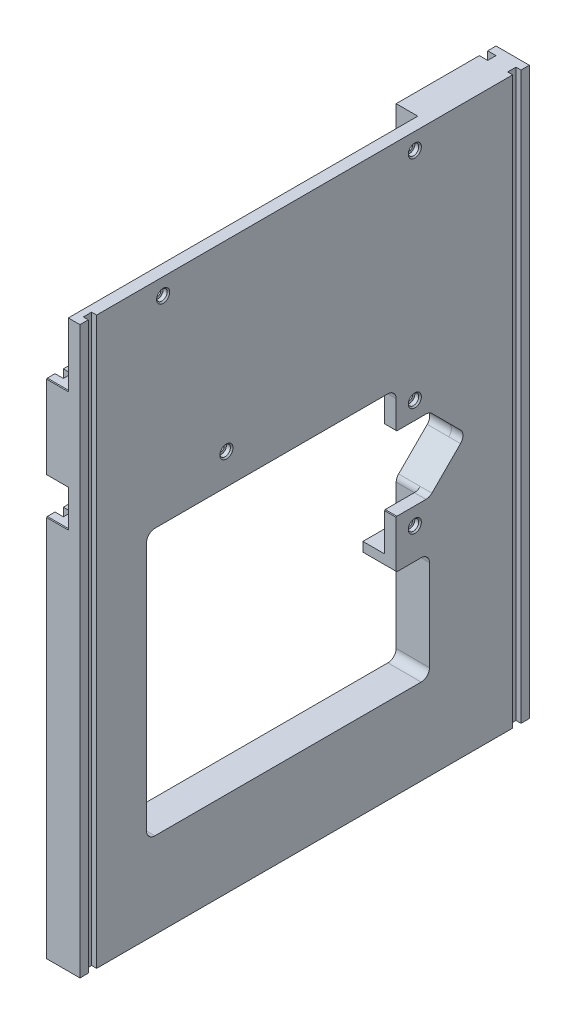
SolidWorks part; units mm, degrees
ref_plane "Front Plane" through (0, 0, 0) normal (0, 0, 1) x (1, 0, 0)
ref_plane "Top Plane" through (0, 0, 0) normal (0, 1, 0) x (1, 0, 0)
ref_plane "Right Plane" through (0, 0, 0) normal (1, 0, 0) x (0, 0, -1)
sketch "Sketch2" plane through (0, 0, 0) normal (1, 0, 0) x (0, 0, -1)
  line L1 (-215.489, 137.2751) -> (127.411, 137.2751)
  line L2 (-215.489, 137.2751) -> (-215.489, -294.5249)
  line L3 (-215.489, -294.5249) -> (127.411, -294.5249)
  line L4 (127.411, 137.2751) -> (127.411, -294.5249)
  dimension "D1" = 342.9
  dimension "D2" = 431.8
extrude "Base" add sketch "Sketch2" along normal blind 25.4
sketch "Sketch3" plane through (0, 0, 0) normal (1, 0, 0) x (0, 0, -1)
  line L0 (-44.039, -294.5249) -> (-44.039, 137.2751) construction
  line L1 (-215.489, -294.5249) -> (127.411, -294.5249) construction
  line L2 (-164.689, -25.9199) -> (-164.689, -229.1199)
  line L3 (-164.689, -229.1199) -> (51.211, -229.1199)
  line L4 (51.211, -146.9509) -> (51.211, -229.1199)
  line L5 (127.411, 137.2751) -> (-215.489, 137.2751) construction
  line L7 (-215.489, 137.2751) -> (-215.489, -294.5249) construction
  line L9 (51.211, -146.9509) -> (25.811, -146.9509)
  line L13 (-164.689, -25.9199) -> (25.811, -25.9199)
  line L14 (25.811, -146.9509) -> (25.811, -25.9199)
  dimension "D1" = 25.4
  dimension "D2" = 163.195
  dimension "D3" = 50.8
  dimension "D4" = 121.031
  dimension "D5" = 190.5
  dimension "D6" = 203.2
extrude "Cut-Extrude3" cut sketch "Sketch3" along normal up to next
sketch "Sketch4" plane through (0, 0, 0) normal (1, 0, 0) x (0, 0, -1)
  line L0 (-215.489, 137.2751) -> (-215.489, -294.5249) construction
  line L1 (19.461, -18.2999) -> (-158.339, -18.2999)
  line L2 (51.211, -15.1249) -> (51.211, 137.2751)
  line L3 (51.211, 137.2751) -> (-202.789, 137.2751)
  line L4 (-164.689, -12.5837) -> (-164.689, -2.4249)
  line L5 (51.211, -146.9509) -> (25.811, -146.9509) construction
  line L6 (25.811, -25.9199) -> (-164.689, -25.9199) construction
  line L7 (-164.689, 24.8801) -> (-215.489, 24.8801)
  line L8 (51.211, -15.1249) -> (51.211, -53.8599)
  line L9 (44.861, -139.3309) -> (25.811, -139.3309)
  line L10 (25.811, -25.9199) -> (25.811, -139.3309)
  line L11 (25.811, -25.9199) -> (-164.689, -25.9199) construction
  line L12 (25.811, -25.9199) -> (19.461, -25.9199)
  line L13 (19.461, -18.2999) -> (19.461, -25.9199)
  line L14 (51.211, -136.1559) -> (51.211, -146.9509)
  line L15 (51.211, -146.9509) -> (44.861, -146.9509)
  line L16 (44.861, -139.3309) -> (44.861, -146.9509)
  line L17 (-44.039, 137.2751) -> (-44.039, -294.5249) construction
  line L18 (-164.689, -12.5837) -> (-164.689, -25.9199)
  line L19 (-164.689, -25.9199) -> (-158.339, -25.9199)
  line L20 (-158.339, -18.2999) -> (-158.339, -25.9199)
  line L22 (-215.489, -294.5249) -> (127.411, -294.5249) construction
  line L23 (51.211, -110.2479) -> (79.405, -82.0539)
  line L24 (-164.689, -2.4249) -> (-215.489, -2.4249)
  line L25 (-215.489, 24.8801) -> (-215.489, -2.4249)
  line L26 (-164.689, 24.8801) -> (-164.689, 89.0151)
  line L27 (-202.789, 137.2751) -> (-215.489, 137.2751)
  line L28 (79.405, -82.0539) -> (51.211, -53.8599)
  line L29 (-164.689, 89.0151) -> (-215.489, 89.0151)
  line L30 (-215.489, 137.2751) -> (-215.489, 90.2851)
  line L31 (-215.489, 90.2851) -> (-215.489, 89.0151)
  line L32 (51.211, -110.2479) -> (51.211, -136.1559)
  dimension "D2" = 7.62
  dimension "D3" = 15.875
  dimension "D4" = 276.606
  dimension "D5" = 25.4
  dimension "D6" = 6.35
  dimension "D7" = 6.35
  dimension "D8" = 7.62
  dimension "D9" = 6.35
  dimension "D10" = 48.26
  dimension "D11" = 43.18
  dimension "D12" = 215.9
  dimension "D13" = 266.7
  dimension "D15" = 45
  dimension "D16" = 29.083
  dimension "D17" = 56.388
extrude "NC pocket" cut sketch "Sketch4" along normal blind 16.51
fillet "Fillet9" radius 6.35 2 edges at (8.255, -110.2479, -51.211) (8.255, -53.8599, -51.211)
fillet "Fillet6" radius 6.35 1 edges at (8.255, -82.0539, -79.405)
hole_wizard "CBORE for M4 SHCS1" positions "Sketch8" profile "Sketch10" counterbore size "M4" standard "ANSI Metric" end condition up to next
sketch "Sketch8" plane through (25.4, 0, 0) normal (1, 0, 0) x (0, 0, -1)
  line L1 (127.411, 137.2751) -> (-215.489, 137.2751) construction
  line L4 (-164.689, -2.4249) -> (-164.689, -229.1199) construction
  line L5 (51.211, -229.1199) -> (51.211, -112.8782) construction
  line L6 (-158.339, -18.2999) -> (19.461, -18.2999) construction
  point P0 (-151.989, 124.5751)
  point P5 (40.035, 124.5751)
  point P7 (40.035, -123.4559)
  point P9 (40.035, -40.5249)
  point P11 (-103.729, -2.4249)
  dimension "D2" = 12.7
  dimension "D3" = 12.7
  dimension "D4" = 11.176
  dimension "D5" = 60.96
  dimension "D6" = 15.875
  dimension "D7" = 11.176
  dimension "D8" = 165.1
  dimension "D9" = 11.176
  dimension "D10" = 82.931
  dimension "D11" = 12.7
sketch "Sketch10" plane through (25.4, 124.5751, 151.989) normal (0, 1, 0) x (0, 0, -1)
  line L0 (0, 0) -> (0, 8.89)
  line L1 (0, 8.89) -> (2.15, 8.89)
  line L3 (2.15, 8.89) -> (2.15, 4)
  line L4 (4, 4) -> (2.15, 4)
  line L5 (4, 4) -> (4, 1)
  line L6 (4, 1) -> (5, 0)
  line L7 (5, 0) -> (0, 0)
  line L8 (-4, 1) -> (-5, 0) construction
  line L11 (0, -6.35) -> (0, 107.95) construction
  dimension "Thru Hole Dia." = 4.3
  dimension "Thru Hole Depth" = 8.89
  dimension "C'Bore Dia." = 8
  dimension "C'Bore Depth" = 4
  dimension "Near C'Sink Dia." = 10
  dimension "Near C'Sink Angle" = 90
sketch "Sketch18" plane through (16.51, 0, 0) normal (-1, 0, 0) x (0, 0, 1)
  circle A0 centre (-40.035, 124.5751) radius 7.1755
  circle A1 centre (151.989, 124.5751) radius 7.1755
  circle A2 centre (103.729, -2.4249) radius 7.1755
  circle A3 centre (-40.035, -40.5249) radius 7.1755
  circle A4 centre (-40.035, -123.4559) radius 7.1755
  dimension "D1" = 14.351
  dimension "D2" = 14.351
  dimension "D3" = 14.351
  dimension "D4" = 14.351
  dimension "D5" = 14.351
extrude "Cut-Extrude4" cut sketch "Sketch18" against normal blind 1.016
hole_wizard "3/8-16 Tapped Hole1" positions "3DSketch1" profile "Sketch14" tap size "3/8-16" standard "ANSI Inch"
sketch3d "3DSketch1"
  line L0 (0, -294.5249, 215.489) -> (0, -294.5249, -127.411) construction
  line L1 (25.4, -294.5249, 215.489) -> (0, -294.5249, 215.489) construction
  point P0 (12.7, -294.5249, -70.261)
  point P2 (12.7, -294.5249, 44.039)
  point P4 (12.7, -294.5249, 158.339)
  dimension "D1" = 12.7
  dimension "D2" = 12.7
  dimension "D3" = 12.7
  dimension "D4" = 114.3
  dimension "D6" = 114.3
  dimension "D5" = 171.45
sketch "Sketch14" plane through (12.7, -294.5249, -70.261) normal (1, 0, 0) x (0, 0, -1)
  line L0 (0, 0) -> (0, 30.3247)
  line L1 (0, 30.3247) -> (3.9687, 27.94)
  line L2 (3.9687, 27.94) -> (3.9687, 0)
  line L5 (3.9687, 0) -> (0, 0)
  line L10 (0, 30.3247) -> (-3.9688, 27.94) construction
  line L11 (0, -6.35) -> (0, 107.95) construction
  dimension "Tap Drill Dia." = 7.9375
  dimension "Tap Drill Depth" = 27.94
  dimension "Drill Angle" = 118
cosmetic thread "Hole Thread1" parameters "D1"=25.4, "D2"=9.525
cosmetic thread "Hole Thread2" parameters "D1"=25.4, "D2"=9.525
cosmetic thread "Hole Thread3" parameters "D1"=25.4, "D2"=9.525
hole_wizard "3/8-16 Tapped Hole2" positions "Sketch15" profile "Sketch17" tap size "3/8-16" standard "ANSI Inch"
sketch "Sketch15" plane through (0, 0, 0) normal (-1, 0, 0) x (0, 0, 1)
  line L0 (215.489, -2.4249) -> (215.489, -294.5249) construction
  line L1 (-127.411, -294.5249) -> (-127.411, 137.2751) construction
  line L2 (215.489, -294.5249) -> (-127.411, -294.5249) construction
  point P0 (190.089, -220.8649)
  point P2 (190.089, -162.4449)
  point P4 (-102.011, -220.8649)
  point P6 (-102.011, -162.4449)
  dimension "D1" = 25.4
  dimension "D2" = 25.4
  dimension "D3" = 25.4
  dimension "D4" = 25.4
  dimension "D5" = 73.66
  dimension "D6" = 58.42
  dimension "D7" = 58.42
  dimension "D8" = 73.66
cosmetic thread "Hole Thread4" parameters "D1"=17.78, "D2"=9.525
cosmetic thread "Hole Thread5" parameters "D1"=17.78, "D2"=9.525
cosmetic thread "Hole Thread6" parameters "D1"=17.78, "D2"=9.525
cosmetic thread "Hole Thread7" parameters "D1"=17.78, "D2"=9.525
sketch "Sketch17" plane through (0, -220.8649, 190.089) normal (0, 1, 0) x (0, 0, 1)
  line L0 (0, 0) -> (0, 22.7047)
  line L1 (0, 22.7047) -> (3.9687, 20.32)
  line L2 (3.9687, 20.32) -> (3.9687, 0)
  line L5 (3.9687, 0) -> (0, 0)
  line L10 (0, 22.7047) -> (-3.9688, 20.32) construction
  line L11 (0, -6.35) -> (0, 107.95) construction
  dimension "Tap Drill Dia." = 7.9375
  dimension "Tap Drill Depth" = 20.32
  dimension "Drill Angle" = 118
sketch "Sketch20" plane through (16.51, 0, 0) normal (-1, 0, 0) x (0, 0, 1)
  line L0 (-51.211, -53.8599) -> (-25.811, -53.8599)
  line L2 (-51.211, -53.8599) -> (-79.405, -82.0539)
  line L3 (-79.405, -82.0539) -> (-51.211, -110.2479)
  line L4 (-25.811, -25.9199) -> (-25.811, -139.3309) construction
  line L6 (-25.811, -53.8599) -> (-25.811, -110.2479)
  line L7 (-25.811, -110.2479) -> (-51.211, -110.2479)
  line L8 (-51.211, -45.3946) -> (-51.211, -54.9122) construction
  line L9 (-51.211, -51.2297) -> (-51.211, 137.2751) construction
  line L10 (-51.211, -116.8371) -> (-51.211, -107.9924) construction
  line L11 (-51.211, -146.9509) -> (-51.211, -112.8782) construction
  line L12 (-74.9149, -77.5638) -> (-53.0709, -55.7198) construction
  line L13 (-53.0709, -108.388) -> (-74.9149, -86.544) construction
extrude "Cut-Extrude5" cut sketch "Sketch20" against normal up to next
fillet "Fillet1" radius 6.35 5 edges at (20.955, -25.9199, 164.689) (12.7, -229.1199, 164.689) (12.7, -229.1199, -51.211) (20.955, -146.9509, -51.211) (20.955, -25.9199, -25.811)
fillet "Fillet2" radius 6.35 3 edges at (20.955, -82.0539, -79.405) (20.955, -110.2479, -51.211) (20.955, -53.8599, -51.211)
chamfer "Chamfer1" distance 0.508 angle 45 9 edges at (8.255, -2.4249, 215.489) (8.255, -2.4249, 164.689) (8.255, 24.8801, 215.489) (8.255, 24.8801, 164.689) (8.255, 89.0151, 215.489) (8.255, 89.0151, 164.689) (12.7, -146.9509, -25.811) (20.955, -110.2479, -25.811) (20.955, -53.8599, -25.811)
sketch "Sketch21" plane through (0, 0, 0) normal (-1, 0, 0) x (0, 0, 1)
  line L0 (215.489, -294.5249) -> (-127.411, -294.5249) construction
  line L1 (209.139, -294.5249) -> (202.789, -294.5249)
  line L2 (209.139, -294.5249) -> (209.139, 137.2751)
  line L3 (209.139, 137.2751) -> (202.789, 137.2751)
  line L4 (202.789, -294.5249) -> (202.789, 137.2751)
  line L5 (-127.411, 137.2751) -> (-51.211, 137.2751) construction
  line L6 (215.489, -2.9329) -> (215.489, -294.5249) construction
  line L7 (-127.411, -294.5249) -> (-127.411, 137.2751) construction
  line L8 (-114.711, -294.5249) -> (-121.061, -294.5249)
  line L9 (-114.711, -294.5249) -> (-114.711, 137.2751)
  line L10 (-114.711, 137.2751) -> (-121.061, 137.2751)
  line L11 (-121.061, -294.5249) -> (-121.061, 137.2751)
  dimension "D1" = 6.35
  dimension "D2" = 6.35
  dimension "D3" = 6.35
  dimension "D4" = 6.35
extrude "Cut-Extrude6" cut sketch "Sketch21" against normal blind 6.35
sketch "Sketch22" plane through (25.4, 0, 0) normal (1, 0, 0) x (0, 0, -1)
  line L0 (-215.489, -294.5249) -> (127.411, -294.5249) construction
  line L1 (-202.789, -294.5249) -> (-209.139, -294.5249)
  line L2 (-202.789, -294.5249) -> (-202.789, 137.2751)
  line L3 (-202.789, 137.2751) -> (-209.139, 137.2751)
  line L4 (-209.139, -294.5249) -> (-209.139, 137.2751)
  line L5 (127.411, 137.2751) -> (-215.489, 137.2751) construction
  line L6 (-215.489, 137.2751) -> (-215.489, -294.5249) construction
  line L7 (127.411, -294.5249) -> (127.411, 137.2751) construction
  line L8 (114.711, 137.2751) -> (121.061, 137.2751)
  line L9 (114.711, 137.2751) -> (114.711, -294.5249)
  line L10 (114.711, -294.5249) -> (121.061, -294.5249)
  line L11 (121.061, 137.2751) -> (121.061, -294.5249)
  dimension "D1" = 6.35
  dimension "D2" = 6.35
  dimension "D3" = 6.35
  dimension "D4" = 6.35
extrude "Cut-Extrude7" cut sketch "Sketch22" against normal blind 3.81
sketch "Sketch23" plane through (25.4, 0, 0) normal (1, 0, 0) x (0, 0, -1)
  line L0 (40.035, -123.4559) -> (40.035, -40.5249) construction
  line L1 (40.035, -113.1031) -> (71.1477, -81.9904)
  line L2 (40.035, -113.1031) -> (8.9223, -81.9904)
  line L3 (71.1477, -81.9904) -> (40.035, -50.8777)
  line L4 (8.9223, -81.9904) -> (40.035, -50.8777)
  line L5 (40.035, -113.1031) -> (40.035, -50.8777) construction
  line L6 (71.1477, -81.9904) -> (8.9223, -81.9904) construction
  circle A0 centre (40.035, -40.5249) radius 5 construction
  circle A1 centre (40.035, -40.5249) radius 5 construction
  circle A2 centre (40.035, -123.4559) radius 5 construction
  circle A3 centre (40.035, -123.4559) radius 5 construction
  point P6 (0, 0)
  point P7 (40.035, -81.9904)
  point P8 (40.035, -81.9904)
  point P9 (0, 0)
  dimension "D1" = 44
  dimension "D2" = 44
equation "\"D2@Sketch23\"=\"D1@Sketch23\""
